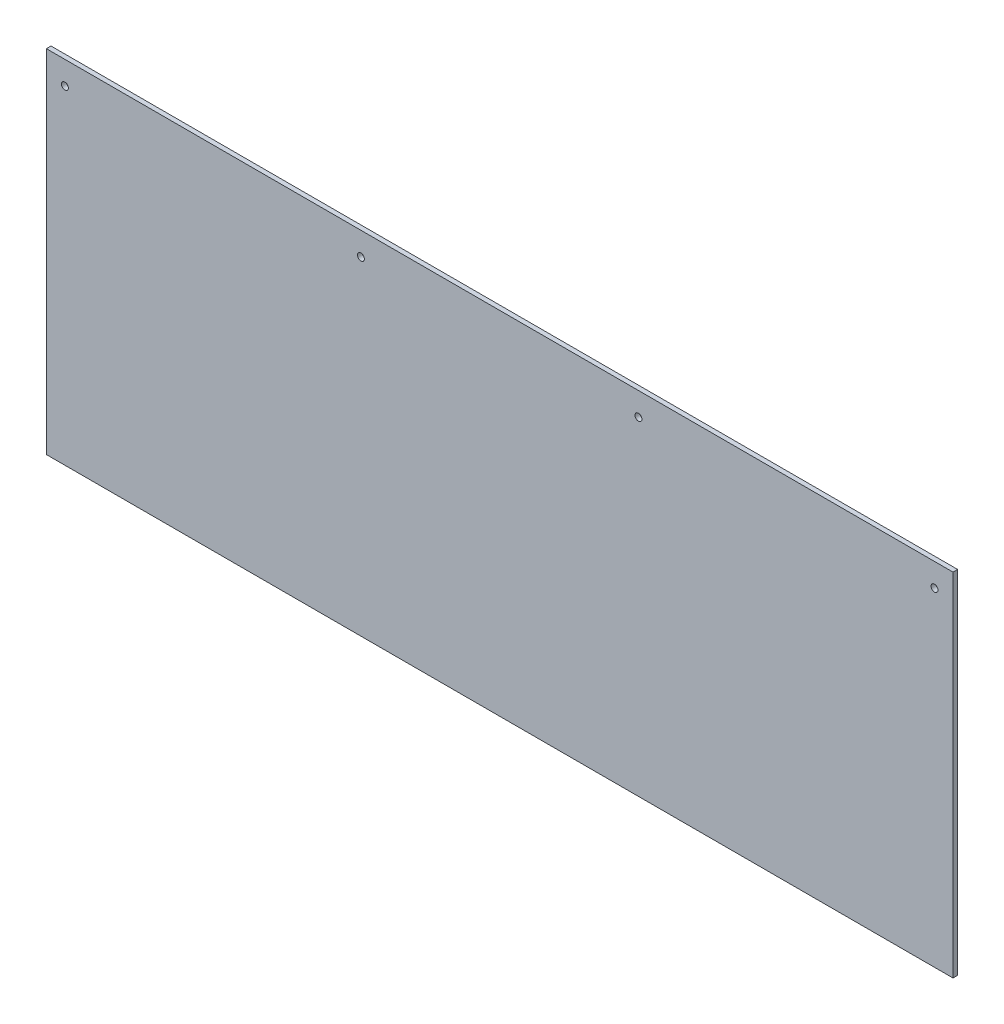
SolidWorks part; units mm, degrees
material "PC High Viscosity"
ref_plane "Front Plane" through (0, 0, 0) normal (0, 0, 1) x (1, 0, 0)
ref_plane "Top Plane" through (0, 0, 0) normal (0, 1, 0) x (1, 0, 0)
ref_plane "Right Plane" through (0, 0, 0) normal (1, 0, 0) x (0, 0, -1)
sketch "Sketch1" plane through (0, 0, 0) normal (0, 0, 1) x (1, 0, 0)
  line L1 (0, 0) -> (1244.6, 0)
  line L2 (0, 0) -> (0, 482.6)
  line L3 (0, 482.6) -> (1244.6, 482.6)
  line L4 (1244.6, 0) -> (1244.6, 482.6)
  dimension "D1" = 482.6
  dimension "D2" = 1244.6
extrude "Boss-Extrude1" add sketch "Sketch1" along normal blind 6.35
sketch "Sketch2" plane through (0, 0, 6.35) normal (0, 0, 1) x (1, 0, 0)
  line L0 (1244.6, 482.6) -> (0, 482.6) construction
  line L1 (0, 482.6) -> (0, 0) construction
  circle A0 centre (25.4, 450.85) radius 4.7625
  circle A1 centre (431.8, 450.85) radius 4.7625
  circle A2 centre (812.8, 450.85) radius 4.7625
  circle A3 centre (1219.2, 450.85) radius 4.7625
  dimension "D1" = 9.525
  dimension "D4" = 431.8
  dimension "D5" = 812.8
  dimension "D6" = 1219.2
  dimension "D2" = 31.75
  dimension "D3" = 25.4
extrude "Cut-Extrude1" cut sketch "Sketch2" against normal through all
